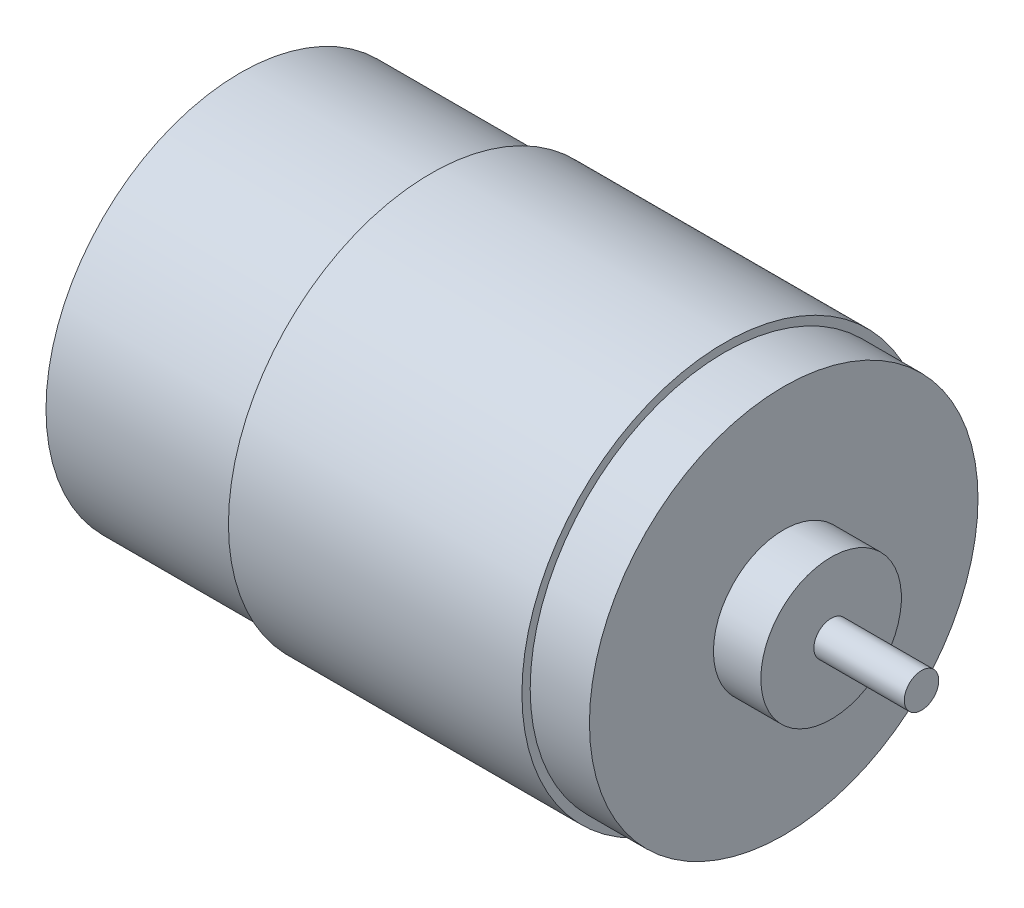
SolidWorks part; units mm, degrees
ref_plane "Front Plane" through (0, 0, 0) normal (0, 0, 1) x (1, 0, 0)
ref_plane "Top Plane" through (0, 0, 0) normal (0, 1, 0) x (1, 0, 0)
ref_plane "Right Plane" through (0, 0, 0) normal (1, 0, 0) x (0, 0, -1)
sketch "Sketch1" plane through (0, 0, 0) normal (0, 0, 1) x (1, 0, 0)
  line L0 (-37.6388, 0) -> (28.1887, 0) construction
  line L1 (-29.8041, 0) -> (-29.8041, 1.5346)
  line L2 (-29.8041, 1.5346) -> (-28.9156, 1.5346)
  line L3 (-28.9156, 1.5346) -> (-28.9156, 2.6654)
  line L4 (-28.9156, 2.6654) -> (-27.6233, 2.6654)
  line L5 (-27.6233, 2.6654) -> (-27.6233, 4.7654)
  line L6 (-27.6233, 4.7654) -> (-26.6944, 5.6943)
  line L7 (-26.6944, 5.6943) -> (-24.6479, 5.6943)
  line L8 (-24.6479, 5.6943) -> (-24.6479, 17.907)
  line L9 (-24.6479, 17.907) -> (-7.0711, 17.907)
  line L10 (-7.0711, 17.907) -> (-7.0711, 18.669)
  line L11 (-7.0711, 18.669) -> (19.9799, 18.669)
  line L12 (19.9799, 18.669) -> (19.9799, 17.907)
  line L13 (19.9799, 17.907) -> (25.4409, 17.907)
  line L14 (25.4409, 17.907) -> (25.4409, 6.477)
  line L15 (25.4409, 6.477) -> (29.8097, 6.477)
  line L16 (29.8097, 6.477) -> (29.8097, 1.5875)
  line L17 (29.8097, 1.5875) -> (38.1409, 1.5875)
  line L18 (38.1409, 1.5875) -> (38.1409, 0)
  line L19 (38.1409, 0) -> (-29.8041, 0)
  dimension "D1" = 37.338
  dimension "D2" = 35.814
  dimension "D3" = 35.814
  dimension "D4" = 12.954
  dimension "D5" = 3.175
  dimension "D6" = 67.945
  dimension "D7" = 8.3312
  dimension "D8" = 4.3688
  dimension "D9" = 5.461
  dimension "D10" = 27.051
  dimension "D11" = 50.0888
revolve "Revolve1" add sketch "Sketch1" angle 360 about L0
